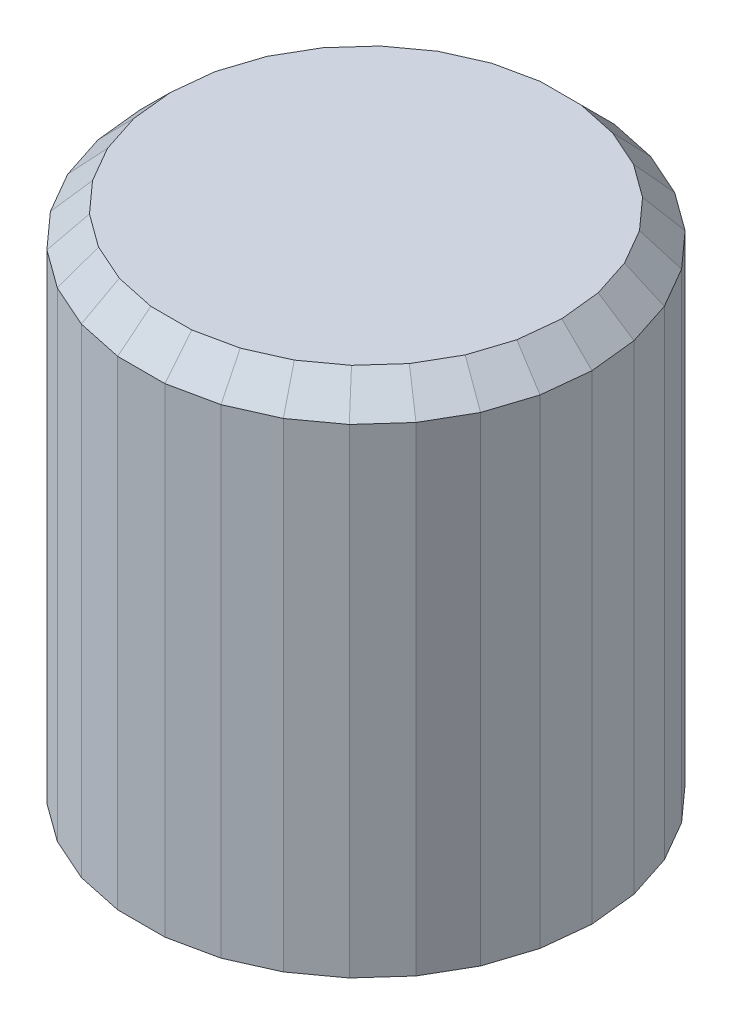
SolidWorks part; units mm, degrees
ref_plane "Front Plane" through (0, 0, 0) normal (0, 0, 1) x (1, 0, 0)
ref_plane "Top Plane" through (0, 0, 0) normal (0, 1, 0) x (1, 0, 0)
ref_plane "Right Plane" through (0, 0, 0) normal (1, 0, 0) x (0, 0, -1)
sketch "Sketch1" plane through (0, 0, 0) normal (0, 1, 0) x (1, 0, 0)
  line L0 (0, -7.5) -> (0, 7.5) construction
  line L1 (-0.7883, 7.5) -> (0.7883, 7.5)
  line L2 (0.7883, 7.5) -> (2.3304, 7.1722)
  line L3 (2.3304, 7.1722) -> (3.7707, 6.531)
  line L4 (3.7707, 6.531) -> (5.0461, 5.6043)
  line L5 (5.0461, 5.6043) -> (6.101, 4.4327)
  line L6 (6.101, 4.4327) -> (6.8893, 3.0673)
  line L7 (6.8893, 3.0673) -> (7.3765, 1.5679)
  line L8 (7.3765, 1.5679) -> (7.5413, 0)
  line L9 (7.5413, 0) -> (7.3765, -1.5679)
  line L10 (7.3765, -1.5679) -> (6.8893, -3.0673)
  line L11 (6.8893, -3.0673) -> (6.101, -4.4327)
  line L12 (6.101, -4.4327) -> (5.0461, -5.6043)
  line L13 (5.0461, -5.6043) -> (3.7707, -6.531)
  line L14 (3.7707, -6.531) -> (2.3304, -7.1722)
  line L15 (2.3304, -7.1722) -> (0.7883, -7.5)
  line L16 (0.7883, -7.5) -> (-0.7883, -7.5)
  line L17 (-0.7883, -7.5) -> (-2.3304, -7.1722)
  line L18 (-2.3304, -7.1722) -> (-3.7707, -6.531)
  line L19 (-3.7707, -6.531) -> (-5.0461, -5.6043)
  line L20 (-5.0461, -5.6043) -> (-6.101, -4.4327)
  line L21 (-6.101, -4.4327) -> (-6.8893, -3.0673)
  line L22 (-6.8893, -3.0673) -> (-7.3765, -1.5679)
  line L23 (-7.3765, -1.5679) -> (-7.5413, 0)
  line L24 (-7.5413, 0) -> (-7.3765, 1.5679)
  line L25 (-7.3765, 1.5679) -> (-6.8893, 3.0673)
  line L26 (-6.8893, 3.0673) -> (-6.101, 4.4327)
  line L27 (-6.101, 4.4327) -> (-5.0461, 5.6043)
  line L28 (-5.0461, 5.6043) -> (-3.7707, 6.531)
  line L29 (-3.7707, 6.531) -> (-2.3304, 7.1722)
  line L30 (-2.3304, 7.1722) -> (-0.7883, 7.5)
  point P4 (0, 0)
  point P8 (0, 7.5)
  point P68 (0, 0)
  dimension "D1" = 15
  dimension "D2" = 30
extrude "Boss-Extrude1" add sketch "Sketch1" along normal blind 12
sketch "Sketch3" plane through (0, 0, 0) normal (0, -1, 0) x (-1, 0, 0)
  line L7 (2.6693, 1.625) -> (-2.6693, 1.625)
  arc A17 (0, -3.125) -> (2.6693, 1.625) centre (0, 0) ccw
  arc A18 (-2.6693, 1.625) -> (0, -3.125) centre (0, 0) ccw
extrude "Cut-Extrude2" cut sketch "Sketch3" against normal blind 10.5
sketch "Sketch4" plane through (0, 0, 0) normal (0, -1, 0) x (-1, 0, 0)
  line L60 (-0.7883, 7.5) -> (-2.3304, 7.1722)
  line L61 (-2.3304, 7.1722) -> (-3.7707, 6.531)
  line L62 (-3.7707, 6.531) -> (-5.0461, 5.6043)
  line L63 (-5.0461, 5.6043) -> (-6.101, 4.4327)
  line L64 (-6.101, 4.4327) -> (-6.8893, 3.0673)
  line L65 (-6.8893, 3.0673) -> (-7.3765, 1.5679)
  line L66 (-7.3765, 1.5679) -> (-7.5413, 0)
  line L67 (-7.5413, 0) -> (-7.3765, -1.5679)
  line L68 (-7.3765, -1.5679) -> (-6.8893, -3.0673)
  line L69 (-6.8893, -3.0673) -> (-6.101, -4.4327)
  line L70 (-6.101, -4.4327) -> (-5.0461, -5.6043)
  line L71 (-5.0461, -5.6043) -> (-3.7707, -6.531)
  line L72 (-3.7707, -6.531) -> (-2.3304, -7.1722)
  line L73 (-2.3304, -7.1722) -> (-0.7883, -7.5)
  line L74 (-0.7883, -7.5) -> (0.7883, -7.5)
  line L75 (0.7883, -7.5) -> (2.3304, -7.1722)
  line L76 (2.3304, -7.1722) -> (3.7707, -6.531)
  line L77 (3.7707, -6.531) -> (5.0461, -5.6043)
  line L78 (5.0461, -5.6043) -> (6.101, -4.4327)
  line L79 (6.101, -4.4327) -> (6.8893, -3.0673)
  line L80 (6.8893, -3.0673) -> (7.3765, -1.5679)
  line L81 (7.3765, -1.5679) -> (7.5413, 0)
  line L82 (7.5413, 0) -> (7.3765, 1.5679)
  line L83 (7.3765, 1.5679) -> (6.8893, 3.0673)
  line L84 (6.8893, 3.0673) -> (6.101, 4.4327)
  line L85 (6.101, 4.4327) -> (5.0461, 5.6043)
  line L86 (5.0461, 5.6043) -> (3.7707, 6.531)
  line L87 (3.7707, 6.531) -> (2.3304, 7.1722)
  line L88 (2.3304, 7.1722) -> (0.7883, 7.5)
  line L89 (0.7883, 7.5) -> (-0.7883, 7.5)
  line L90 (-0.7883, 7.5) -> (-2.3304, 7.1722)
  line L91 (-2.3304, 7.1722) -> (-3.7707, 6.531)
  line L92 (-3.7707, 6.531) -> (-5.0461, 5.6043)
  line L93 (-5.0461, 5.6043) -> (-6.101, 4.4327)
  line L94 (-6.101, 4.4327) -> (-6.8893, 3.0673)
  line L95 (-6.8893, 3.0673) -> (-7.3765, 1.5679)
  line L96 (-7.3765, 1.5679) -> (-7.5413, 0)
  line L97 (-7.5413, 0) -> (-7.3765, -1.5679)
  line L98 (-7.3765, -1.5679) -> (-6.8893, -3.0673)
  line L99 (-6.8893, -3.0673) -> (-6.101, -4.4327)
  line L100 (-6.101, -4.4327) -> (-5.0461, -5.6043)
  line L101 (-5.0461, -5.6043) -> (-3.7707, -6.531)
  line L102 (-3.7707, -6.531) -> (-2.3304, -7.1722)
  line L103 (-2.3304, -7.1722) -> (-0.7883, -7.5)
  line L104 (-0.7883, -7.5) -> (0.7883, -7.5)
  line L105 (0.7883, -7.5) -> (2.3304, -7.1722)
  line L106 (2.3304, -7.1722) -> (3.7707, -6.531)
  line L107 (3.7707, -6.531) -> (5.0461, -5.6043)
  line L108 (5.0461, -5.6043) -> (6.101, -4.4327)
  line L109 (6.101, -4.4327) -> (6.8893, -3.0673)
  line L110 (6.8893, -3.0673) -> (7.3765, -1.5679)
  line L111 (7.3765, -1.5679) -> (7.5413, 0)
  line L112 (7.5413, 0) -> (7.3765, 1.5679)
  line L113 (7.3765, 1.5679) -> (6.8893, 3.0673)
  line L114 (6.8893, 3.0673) -> (6.101, 4.4327)
  line L115 (6.101, 4.4327) -> (5.0461, 5.6043)
  line L116 (5.0461, 5.6043) -> (3.7707, 6.531)
  line L117 (3.7707, 6.531) -> (2.3304, 7.1722)
  line L118 (2.3304, 7.1722) -> (0.7883, 7.5)
  line L119 (0.7883, 7.5) -> (-0.7883, 7.5)
  arc A7 (-4, 0) -> (4, 0) centre (0, 0) ccw
  arc A8 (4, 0) -> (-4, 0) centre (0, 0) ccw
  dimension "D1" = 0
extrude "Boss-Extrude2" add sketch "Sketch4" along normal blind 5
chamfer "Chamfer1" distance 1 angle 45 30 edges at (-5.5736, 12, -5.0185) (-4.4084, 12, -6.0676) (-3.0505, 12, -6.8516) (-1.5593, 12, -7.3361) (0, 12, -7.5) (1.5593, 12, -7.3361) (3.0505, 12, -6.8516) (4.4084, 12, -6.0676) (5.5736, 12, -5.0185) (6.4952, 12, -3.75) (7.1329, 12, -2.3176) (7.4589, 12, -0.784) (7.4589, 12, 0.784) (7.1329, 12, 2.3176) (6.4952, 12, 3.75) (5.5736, 12, 5.0185) (4.4084, 12, 6.0676) (3.0505, 12, 6.8516) (1.5593, 12, 7.3361) (0, 12, 7.5) (-1.5593, 12, 7.3361) (-3.0505, 12, 6.8516) (-4.4084, 12, 6.0676) (-5.5736, 12, 5.0185) (-6.4952, 12, 3.75) (-7.1329, 12, 2.3176) (-7.4589, 12, 0.784) (-7.4589, 12, -0.784) (-7.1329, 12, -2.3176) (-6.4952, 12, -3.75)
